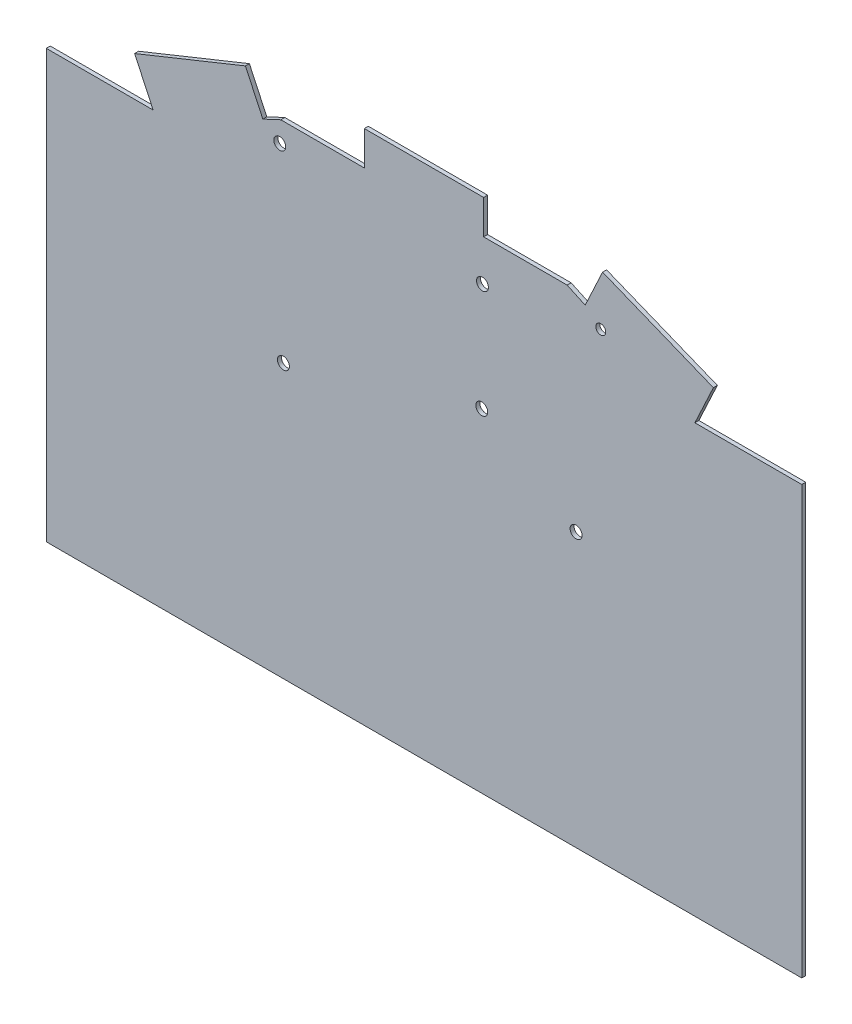
SolidWorks part; units mm, degrees
material "Acrílico (Impacto medio-alto)"
ref_plane "Alzado" through (0, 0, 0) normal (0, 0, 1) x (1, 0, 0)
ref_plane "Planta" through (0, 0, 0) normal (0, 1, 0) x (1, 0, 0)
ref_plane "Vista lateral" through (0, 0, 0) normal (1, 0, 0) x (0, 0, -1)
sketch "Croquis1" plane through (0, 0, 0) normal (0, 0, 1) x (1, 0, 0)
  line L1 (-95, -65) -> (95, -65)
  line L2 (-95, -65) -> (-95, 65)
  line L3 (-95, 65) -> (95, 65)
  line L4 (95, -65) -> (95, 65)
  line L5 (-95, -65) -> (95, 65) construction
  line L6 (-95, 65) -> (95, -65) construction
  point P0 (0, 0)
  dimension "D1" = 190
  dimension "D2" = 130
extrude "Saliente-Extruir1" add sketch "Croquis1" along normal blind 1 contours L1 L4 L3 L2
sketch "Croquis9" plane through (0, 0, 0) normal (0, 0, -1) x (-1, 0, 0)
  line L0 (-95, 30.1397) -> (-49.45, 30.1397) construction
  line L1 (-95, -65) -> (-95, 65) construction
  line L2 (-49.45, 30.1397) -> (-49.45, 65) construction
  line L3 (-44.45, 51) -> (-38.24, 51) construction
  line L4 (95, -65) -> (-95, -65) construction
  line L5 (95, 30.1397) -> (49.45, 30.1397) construction
  line L6 (95, -65) -> (95, 65) construction
  line L7 (49.45, -65) -> (49.45, 65) construction
  line L8 (95, 65) -> (-95, 65) construction
  line L9 (-49.45, 65) -> (-49.45, 51) construction
  line L10 (-49.45, 51) -> (-44.45, 51) construction
  line L11 (-38.24, 51) -> (-38.24, 3.75) construction
  circle A7 centre (-44.45, 51) radius 1.25
  circle A9 centre (35.3575, 3.7467) radius 1.5
  circle A10 centre (36.2701, 51.1277) radius 1.5
  circle A11 centre (-14.5249, 18.7475) radius 1.5
  circle A12 centre (-14.7004, 45.9873) radius 1.5
  circle A14 centre (-38.24, 3.75) radius 1.5
  dimension "D5" = 3
  dimension "D6" = 2.5
  dimension "D9" = 3
  dimension "D10" = 3
  dimension "D11" = 3
  dimension "D12" = 3
  dimension "D1" = 45.55
  dimension "D2" = 45.55
  dimension "D3" = 14
  dimension "D4" = 5
  dimension "D7" = 6.21
  dimension "D8" = 47.25
extrude "Cortar-Extruir2" cut sketch "Croquis9" against normal blind 10
sketch "Croquis12" plane through (0, 0, 0) normal (0, 0, -1) x (-1, 0, 0)
  line L0 (-95, 65) -> (-95, 43.5)
  line L1 (-95, -65) -> (-95, 65) construction
  line L2 (-95, 43.5) -> (-41.6516, 65)
  line L3 (95, 65) -> (-95, 65) construction
  line L4 (-41.6516, 65) -> (-95, 65)
  line L5 (0, 65) -> (0, 27.1785) construction
  line L6 (41.6516, 65) -> (95, 65)
  line L7 (95, 43.5) -> (41.6516, 65)
  line L8 (95, 65) -> (95, 43.5)
extrude "Cortar-Extruir3" cut sketch "Croquis12" against normal up to next
sketch "Croquis13" plane through (0, 0, 0) normal (0, 0, -1) x (-1, 0, 0)
  line L0 (-68.1232, 42.4822) -> (-72.7746, 52.4571)
  line L1 (-95, 43.5) -> (-41.6516, 65) construction
  line L3 (-44.9098, 63.6869) -> (-40.5315, 54.2978)
  line L4 (-40.5315, 54.2978) -> (-36, 56.4109)
  line L5 (-36, 56.4109) -> (-15, 56.4109)
  line L6 (-15, 56.4109) -> (-15, 65)
  line L7 (41.6516, 65) -> (-41.6516, 65) construction
  line L8 (44.9098, 63.6869) -> (41.6516, 65)
  line L9 (15.0115, 65) -> (15, 56.4109)
  line L10 (15, 56.4109) -> (36, 56.4109)
  line L11 (36, 56.4109) -> (40.5315, 54.2978)
  line L12 (40.5315, 54.2978) -> (44.9098, 63.6869)
  line L13 (41.6516, 65) -> (95, 43.5) construction
  line L15 (72.7746, 52.4571) -> (68.1232, 42.4822)
  line L16 (68.1232, 42.4822) -> (95, 42.4822)
  line L17 (95, -65) -> (95, 43.5) construction
  line L18 (41.6516, 65) -> (15.0115, 65)
  line L19 (-44.9098, 63.6869) -> (-41.6516, 65)
  line L20 (-41.6516, 65) -> (-15, 65)
  line L21 (-72.7746, 52.4571) -> (-95, 43.5)
  line L22 (-95, 43.5) -> (-95.0307, 42.4822)
  line L23 (-95.0307, 42.4822) -> (-68.1232, 42.4822)
  line L24 (72.7746, 52.4571) -> (95, 43.5)
  line L25 (95, 43.5) -> (95, 42.4822)
extrude "Cortar-Extruir4" cut sketch "Croquis13" against normal up to next
